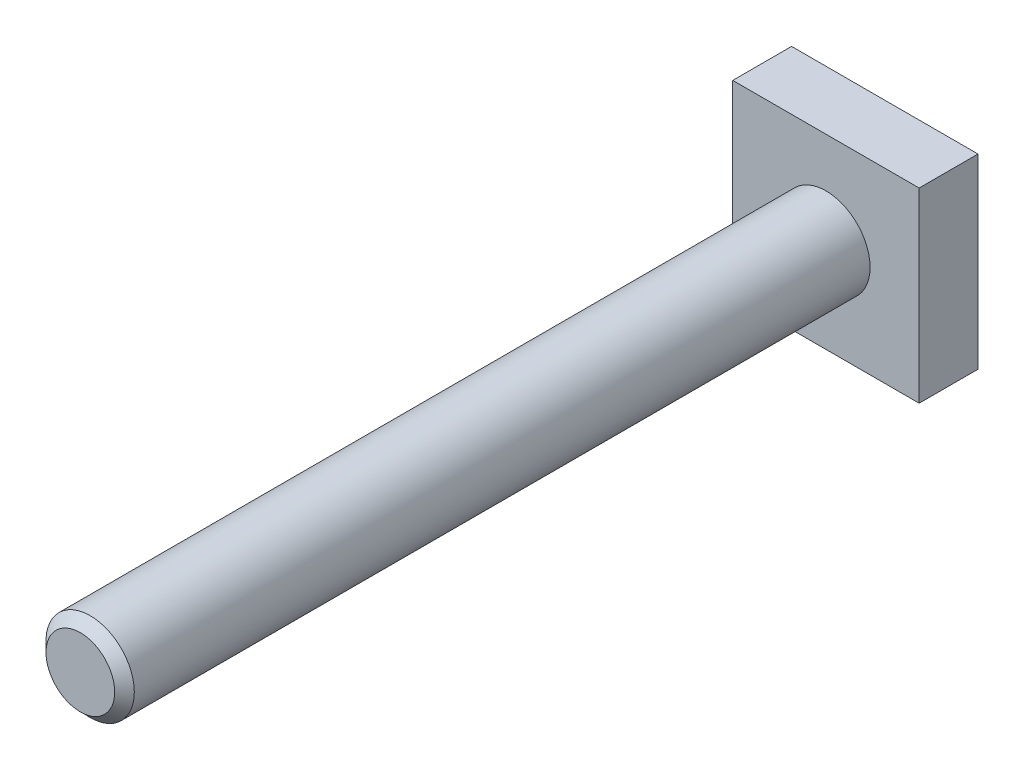
SolidWorks part; units mm, degrees
ref_plane "Front Plane" through (0, 0, 0) normal (0, 0, 1) x (1, 0, 0)
ref_plane "Top Plane" through (0, 0, 0) normal (0, 1, 0) x (1, 0, 0)
ref_plane "Right Plane" through (0, 0, 0) normal (1, 0, 0) x (0, 0, -1)
sketch "Sketch1" plane through (0, 0, 0) normal (0, 0, 1) x (1, 0, 0)
  line L0 (-28.0815, 0) -> (43.1377, 0) construction
  line L2 (-9.5, 9.5) -> (9.5, 9.5)
  line L3 (-9.5, 9.5) -> (-9.5, -9.5)
  line L4 (-9.5, -9.5) -> (9.5, -9.5)
  line L5 (9.5, 9.5) -> (9.5, -9.5)
  line L6 (-9.5, 9.5) -> (9.5, -9.5) construction
  line L7 (-9.5, -9.5) -> (9.5, 9.5) construction
  point P3 (0, 0)
  dimension "D1" = 19
  dimension "D2" = 19
extrude "Boss-Extrude1" add sketch "Sketch1" along normal mid plane 6
sketch "Sketch2" plane through (0, 0, 3) normal (0, 0, 1) x (1, 0, 0)
  circle A0 centre (0, 0) radius 4.5
  dimension "D1" = 9
extrude "Boss-Extrude2" add sketch "Sketch2" along normal blind 76
chamfer "Chamfer1" distance 1 angle 45 1 edges at (4.5, 0, 79)
